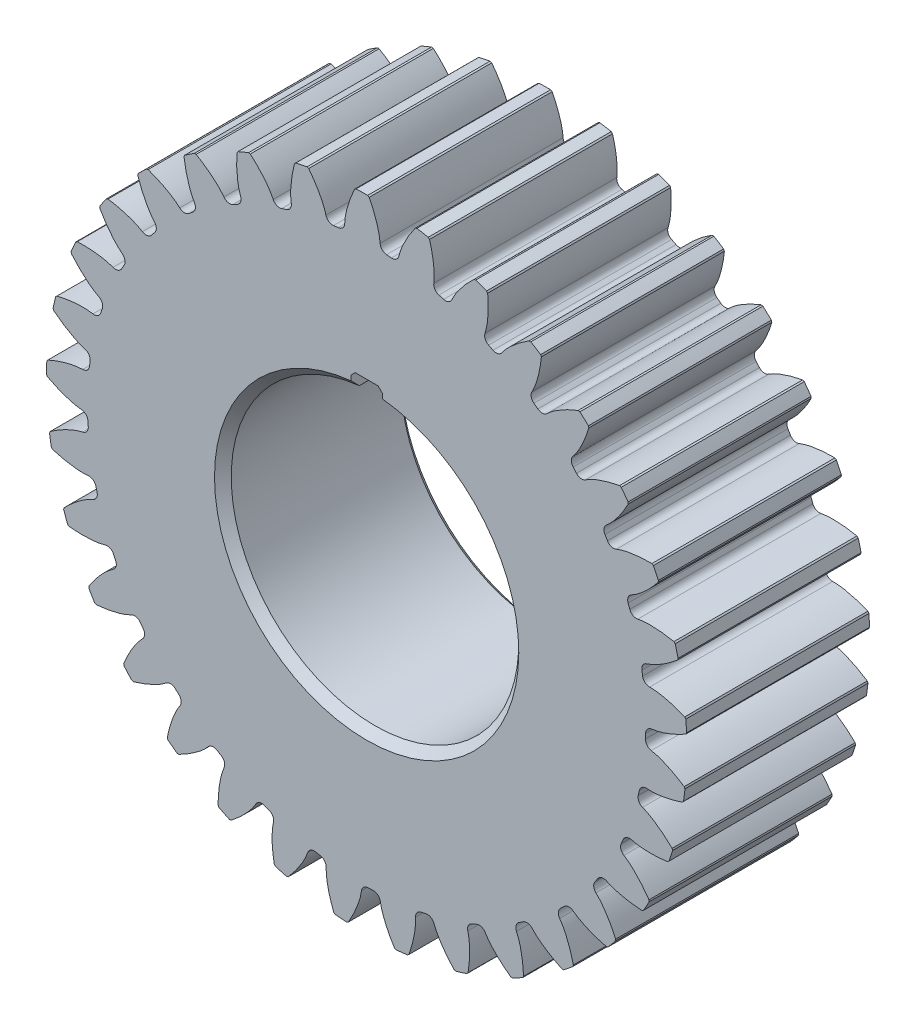
SolidWorks part; units mm, degrees
material "1.6587 (18CrNiMo7-6)"
ref_plane "Front Plane" through (0, 0, 0) normal (0, 0, 1) x (1, 0, 0)
ref_plane "Top Plane" through (0, 0, 0) normal (0, 1, 0) x (1, 0, 0)
ref_plane "Right Plane" through (0, 0, 0) normal (1, 0, 0) x (0, 0, -1)
sketch "Sketch1" plane through (0, 0, 0) normal (0, 0, 1) x (1, 0, 0)
  circle A0 centre (0, 0) radius 57.75 construction
  circle A1 centre (0, 0) radius 53.375
  dimension "D1" = 115.5
  dimension "D2" = 4.375
extrude "Boss-Extrude1" add sketch "Sketch1" along normal blind 35
sketch "Sketch2" plane through (0, 0, 0) normal (0, 0, 1) x (1, 0, 0)
  line L0 (0, 0) -> (57.7436, 0.8607) construction
  line L1 (0, 0) -> (69.9639, 4.3788) construction
  circle A0 centre (0, 0) radius 57.75 construction
  arc A1 (53.3598, -1.2717) -> (52.7849, 7.9148) centre (0, 0) ccw
  arc A2 (61.198, 2.5225) -> (61.035, 5.1275) centre (0, 0) ccw
  arc A3 (54.553, 0.0196) -> (53.3598, -1.2717) centre (54.6895, -1.3034) ccw
  arc A4 (54.1297, 6.7824) -> (52.7849, 7.9148) centre (54.1002, 8.1121) cw
  circle A5 centre (0, 0) radius 61.25 construction
  spline S0 degree 4 poles (54.2672, 0) (54.2793, 0.0001) (54.3134, 0.001) (54.3777, 0.0043) (54.4826, 0.0121) (54.6162, 0.0257) (54.7887, 0.0474) (54.9917, 0.0783) (55.2145, 0.1179) (55.4564, 0.1669) (55.6974, 0.2211) (55.9375, 0.2801) (56.1762, 0.3434) (56.4649, 0.4253) (56.8103, 0.5308) (57.2128, 0.6647) (57.6679, 0.8291) (58.1299, 1.0101) (58.5831, 1.1991) (59.0391, 1.4027) (59.479, 1.6086) (59.9338, 1.8353) (60.3526, 2.0512) (60.8193, 2.3072) (61.1952, 2.5179) (61.6883, 2.8109) (61.9786, 2.9885) (62.3174, 3.2014) (62.4674, 3.2988) (62.5597, 3.3586) knots 0 0 0 0 0 0.005377 0.015084 0.028532 0.04661 0.064855 0.092111 0.119476 0.146842 0.174209 0.201575 0.228941 0.256307 0.307035 0.361767 0.4165 0.471232 0.525964 0.580697 0.635429 0.690161 0.744894 0.799626 0.854358 0.909091 0.954545 1 1 1 1 1 construction
  spline S1 degree 4 poles (54.553, 0.0196) (54.5864, 0.0231) (54.6607, 0.0313) (54.7959, 0.0485) (54.9917, 0.0783) (55.2145, 0.1179) (55.4564, 0.1669) (55.6974, 0.2211) (55.9375, 0.2801) (56.1762, 0.3434) (56.4649, 0.4253) (56.8103, 0.5308) (57.2128, 0.6647) (57.6679, 0.8291) (58.1299, 1.0101) (58.5831, 1.1991) (59.0391, 1.4027) (59.479, 1.6086) (59.9338, 1.8353) (60.3526, 2.0512) (60.7544, 2.2716) (60.9944, 2.4055) (61.1493, 2.4943) (61.198, 2.5225) knots 0.031734 0.031734 0.031734 0.031734 0.031734 0.04661 0.064855 0.092111 0.119476 0.146842 0.174209 0.201575 0.228941 0.256307 0.307035 0.361767 0.4165 0.471232 0.525964 0.580697 0.635429 0.690161 0.744894 0.799626 0.823936 0.823936 0.823936 0.823936 0.823936
  spline S2 degree 4 poles (54.1297, 6.7824) (54.1633, 6.7831) (54.238, 6.7842) (54.3743, 6.784) (54.5723, 6.7788) (54.7983, 6.7674) (55.0445, 6.7489) (55.2904, 6.7252) (55.5359, 6.6965) (55.7806, 6.6635) (56.0773, 6.6183) (56.4331, 6.5567) (56.8492, 6.474) (57.3213, 6.3676) (57.8023, 6.2457) (58.2755, 6.1146) (58.7533, 5.9695) (59.2154, 5.82) (59.695, 5.6517) (60.1374, 5.4898) (60.5636, 5.3212) (60.8184, 5.2183) (60.9831, 5.1494) (61.035, 5.1275) knots 0.031734 0.031734 0.031734 0.031734 0.031734 0.04661 0.064855 0.092111 0.119476 0.146842 0.174209 0.201575 0.228941 0.256307 0.307035 0.361767 0.4165 0.471232 0.525964 0.580697 0.635429 0.690161 0.744894 0.799626 0.823936 0.823936 0.823936 0.823936 0.823936
  dimension "D1" = 115.5
  dimension "D4" = 2.66
  dimension "D5" = 2.727
extrude "Boss-Extrude2" add sketch "Sketch2" along normal blind 35
chamfer "Chamfer1" distance 0.2 2 edges at (61.198, 2.5225, 17.5) (61.035, 5.1275, 17.5)
pattern_circular "CirPattern1" count 33 over 360 about axis through (0, 0, 35) along (0, 0, -1) of "Chamfer1", "Boss-Extrude2"
sketch "Sketch3" plane through (0, 0, 35) normal (0, 0, 1) x (1, 0, 0)
  line L0 (0, 0) -> (0, 30.7) construction
  line L1 (3, 27.3359) -> (3, 30.7)
  line L2 (-3, 27.3359) -> (-3, 30.7)
  line L4 (3, 30.7) -> (-3, 30.7)
  line L5 (3, 0) -> (3, 30.7) construction
  line L6 (-3, 0) -> (-3, 30.7) construction
  arc A0 (-3, 27.3359) -> (3, 27.3359) centre (0, 0) ccw
  dimension "D1" = 55
  dimension "D2" = 30.7
  dimension "D3" = 3
  dimension "D4" = 3
extrude "Cut-Extrude1" cut sketch "Sketch3" against normal blind 35
chamfer "Chamfer2" distance 1.6 1 edges at (0, -27.5, 35)
chamfer "Chamfer3" distance 1 1 edges at (0, -27.5, 0)
chamfer "Chamfer4" distance 0.8 2 edges at (3, 30.7, 17.5) (-3, 30.7, 17.5)
